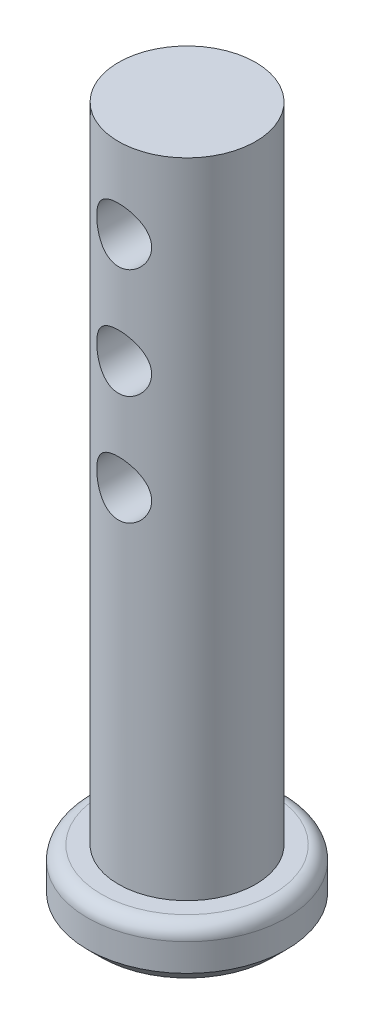
SolidWorks part; units mm, degrees
ref_plane "Front Plane" through (0, 0, 0) normal (0, 0, 1) x (1, 0, 0)
ref_plane "Top Plane" through (0, 0, 0) normal (0, 1, 0) x (1, 0, 0)
ref_plane "Right Plane" through (0, 0, 0) normal (1, 0, 0) x (0, 0, -1)
sketch "Sketch1" plane through (0, 0, 0) normal (0, 1, 0) x (1, 0, 0)
  circle A0 centre (0, 0) radius 4.6037
  dimension "D1" = 9.2075
extrude "Boss-Extrude1" add sketch "Sketch1" along normal blind 2.54
sketch "Sketch2" plane through (0, 2.54, 0) normal (0, 1, 0) x (1, 0, 0)
  circle A0 centre (0, 0) radius 3.175
  dimension "D1" = 6.35
extrude "Boss-Extrude2" add sketch "Sketch2" along normal blind 45.72
sketch "Sketch3" plane through (0, 0, 0) normal (0, 0, 1) x (1, 0, 0)
  line L0 (0, 35.7883) -> (0, -6.2157) construction
  line L1 (4.6037, 2.54) -> (-4.6037, 2.54) construction
  circle A0 centre (0, 18.415) radius 1.27
  circle A1 centre (0, 23.495) radius 1.27
  circle A2 centre (0, 28.575) radius 1.27
  circle A3 centre (0, 33.655) radius 1.27
  circle A4 centre (0, 38.735) radius 1.27
  circle A5 centre (0, 43.815) radius 1.27
  dimension "D1" = 2.54
  dimension "D2" = 15.875
  dimension "D3" = 6
extrude "Cut-Extrude1" cut sketch "Sketch3" against normal through all both and the other way through all
fillet "Fillet1" radius 0.635 1 edges at (0, 2.54, 4.6037)
chamfer "Chamfer1" distance 0.635 angle 45 1 edges at (0, 0, 4.6037)
sketch "Sketch4" plane through (0, 0, 0) normal (1, 0, 0) x (0, 0, -1)
  line L1 (-7.4121, 51.9254) -> (9.4336, 51.9254)
  line L2 (-7.4121, 51.9254) -> (-7.4121, 32.3205)
  line L3 (-7.4121, 32.3205) -> (9.4336, 32.3205)
  line L4 (9.4336, 51.9254) -> (9.4336, 32.3205)
extrude "Cut-Extrude2" cut sketch "Sketch4" against normal through all both and the other way through all
